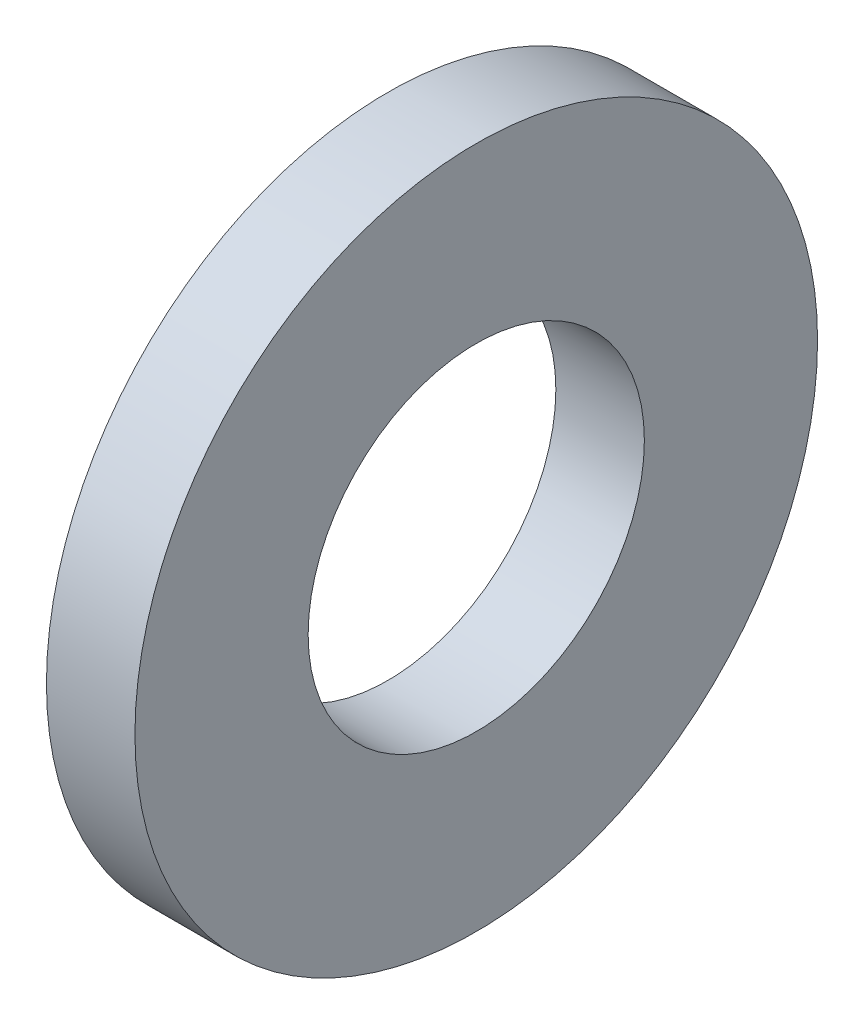
SolidWorks part; units mm, degrees
material "Plain Carbon Steel"
ref_plane "Front Plane" through (0, 0, 0) normal (0, 0, 1) x (1, 0, 0)
ref_plane "Top Plane" through (0, 0, 0) normal (0, 1, 0) x (1, 0, 0)
ref_plane "Right Plane" through (0, 0, 0) normal (1, 0, 0) x (0, 0, -1)
sketch "Sketch1" plane through (0, 0, 0) normal (1, 0, 0) x (0, 0, -1)
  circle A0 centre (0, 0) radius 17.0434
  circle A1 centre (0, 0) radius 8.3947
  dimension "OD" = 34.0868
  dimension "ID" = 16.7894
extrude "Boss-Extrude1" add sketch "Sketch1" along normal blind 4.4196
